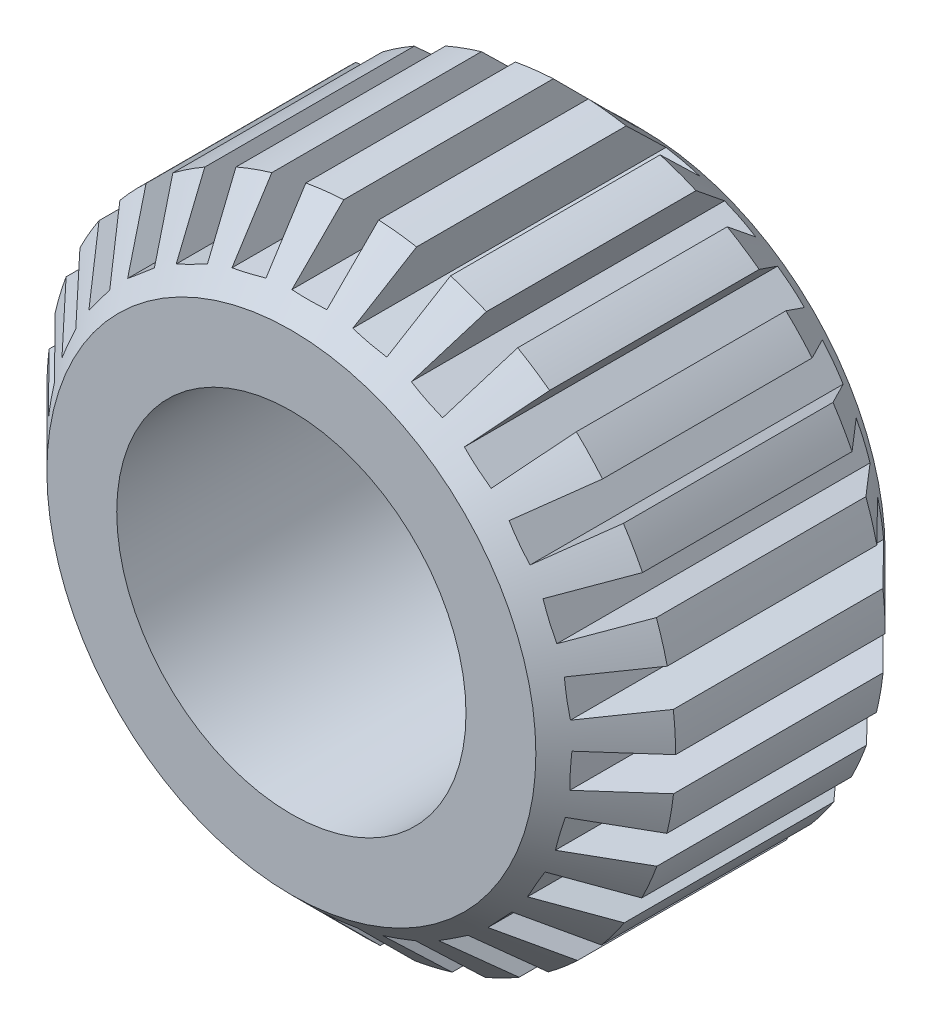
SolidWorks part; units mm, degrees
ref_plane "Front Plane" through (0, 0, 0) normal (0, 0, 1) x (1, 0, 0)
ref_plane "Top Plane" through (0, 0, 0) normal (0, 1, 0) x (1, 0, 0)
ref_plane "Right Plane" through (0, 0, 0) normal (1, 0, 0) x (0, 0, -1)
sketch "Sketch1" plane through (0, 0, 0) normal (0, 0, 1) x (1, 0, 0)
  circle A0 centre (0, 0) radius 5
  circle A1 centre (0, 0) radius 9
  dimension "D1" = 10
  dimension "D2" = 4
extrude "Boss-Extrude1" add sketch "Sketch1" along normal blind 10
chamfer "Chamfer1" distance 2 angle 45 2 edges at (9, 0, 0) (9, 0, 10)
sketch "Sketch2" plane through (0, 0, 0) normal (0, 0, 1) x (1, 0, 0)
  line L0 (0, 0) -> (0, 9) construction
  line L1 (0.5, 7.5) -> (0.5, 8.9861)
  line L2 (-0.5, 7.5) -> (-0.5, 8.9861)
  line L3 (-0.5, 7.5) -> (0.5, 7.5)
  line L4 (0.5, 0) -> (0.5, 9) construction
  line L5 (-0.5, 0) -> (-0.5, 9) construction
  circle A0 centre (0, 0) radius 9 construction
  arc A1 (0.5, 8.9861) -> (-0.5, 8.9861) centre (0, 0) ccw
  dimension "D3" = 7.5
  dimension "D1" = 0.5
  dimension "D2" = 0.5
extrude "Cut-Extrude1" cut sketch "Sketch2" along normal through all contours L2 A1 L1 L3
pattern_circular "CirPattern1" count 27 over 360 about axis through (0, 0, 0) along (0, 0, 1) of "Cut-Extrude1"
scale "Scale1" scale about centroid uniform scaling yes scale factor 2
